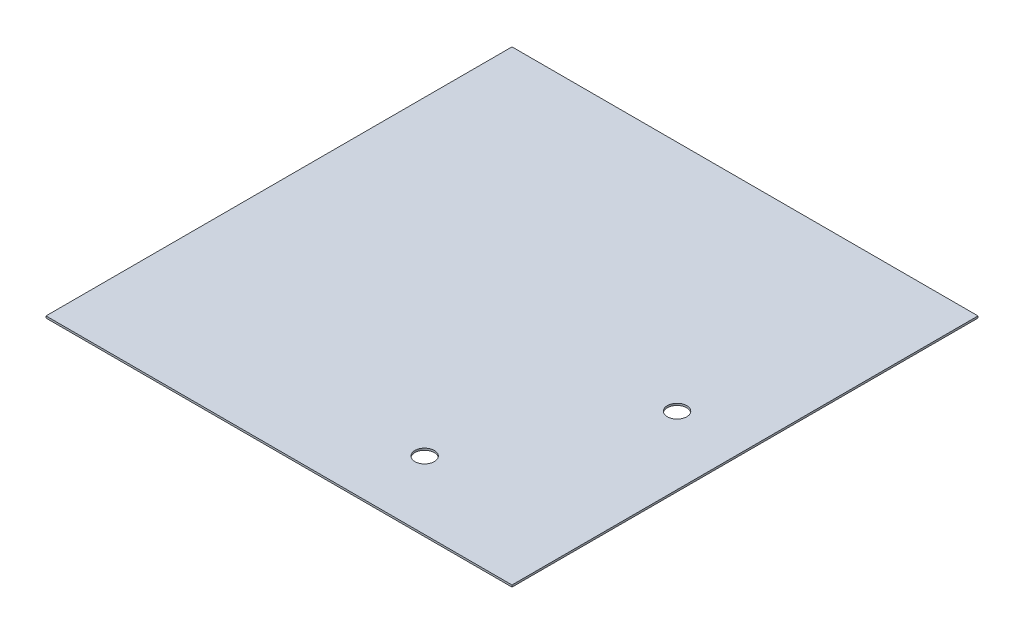
SolidWorks part; units mm, degrees
material "Cedar"
ref_plane "Front Plane" through (0, 0, 0) normal (0, 0, 1) x (1, 0, 0)
ref_plane "Top Plane" through (0, 0, 0) normal (0, 1, 0) x (1, 0, 0)
ref_plane "Right Plane" through (0, 0, 0) normal (1, 0, 0) x (0, 0, -1)
sketch "Sketch1" plane through (0, 0, 0) normal (0, 1, 0) x (1, 0, 0)
  line L1 (-304.8, -304.8) -> (304.8, -304.8)
  line L2 (-304.8, -304.8) -> (-304.8, 304.8)
  line L3 (-304.8, 304.8) -> (304.8, 304.8)
  line L4 (304.8, -304.8) -> (304.8, 304.8)
  line L5 (-304.8, -304.8) -> (304.8, 304.8) construction
  line L6 (-304.8, 304.8) -> (304.8, -304.8) construction
  point P0 (0, 0)
  dimension "D1" = 609.6
  dimension "D2" = 609.6
extrude "Boss-Extrude1" add sketch "Sketch1" along normal blind 2.5
sketch "Sketch2" plane through (0, 2.5, 0) normal (0, 1, 0) x (1, 0, 0)
  line L0 (304.8, -304.8) -> (304.8, 304.8) construction
  line L1 (-304.8, -304.8) -> (304.8, -304.8) construction
  circle A0 centre (101.6, -215.9) radius 12.7
  circle A1 centre (215.9, 0) radius 12.7
  dimension "D1" = 25.4
  dimension "D2" = 25.4
  dimension "D3" = 88.9
  dimension "D4" = 88.9
  dimension "D5" = 203.2
  dimension "D6" = 304.8
extrude "Cut-Extrude1" cut sketch "Sketch2" against normal through all
